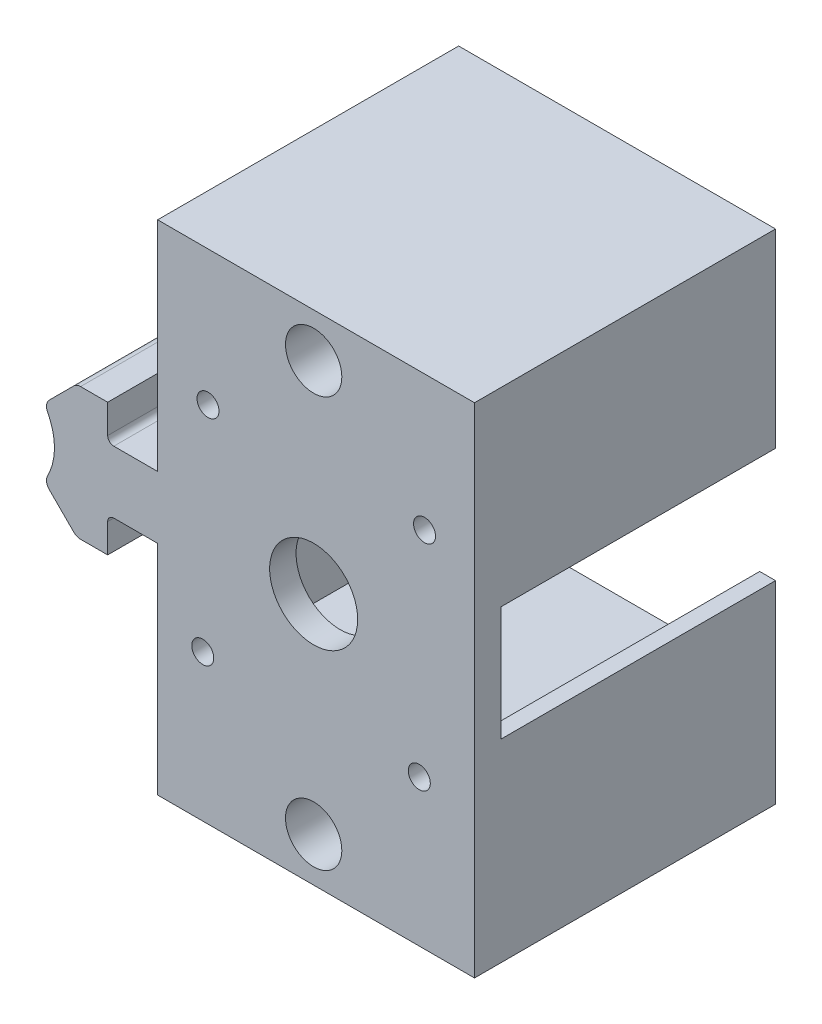
SolidWorks part; units mm, degrees
ref_plane "Front Plane" through (0, 0, 0) normal (0, 0, 1) x (1, 0, 0)
ref_plane "Top Plane" through (0, 0, 0) normal (0, 1, 0) x (1, 0, 0)
ref_plane "Right Plane" through (0, 0, 0) normal (1, 0, 0) x (0, 0, -1)
sketch "Sketch2" plane through (0, 0, 816.4924) normal (0, 0, 1) x (1, 0, 0)
  line L0 (35.7501, 34.0976) -> (35.7501, 33.2853)
  line L27 (48.1133, 38.1834) -> (50.6533, 38.1834)
  line L28 (50.6533, 38.1834) -> (50.6533, 56.9324)
  line L29 (50.6533, 56.9324) -> (52.6853, 56.9324)
  line L30 (52.6853, 56.9324) -> (52.6853, 10.4504)
  line L31 (52.6853, 10.4504) -> (50.6533, 10.4504)
  line L32 (50.6533, 10.4504) -> (50.6533, 29.1994)
  line L33 (50.6533, 29.1994) -> (48.1133, 29.1994)
  line L37 (44.3288, 29.1994) -> (48.1133, 29.1994)
  line L38 (43.4438, 24.1494) -> (43.4438, 28.3144)
  line L39 (39.5326, 24.1494) -> (43.4438, 24.1494)
  line L40 (35.016, 28.0957) -> (38.5589, 24.5527)
  line L41 (35.4657, 33.6914) -> (35.7501, 33.2853)
  line L42 (35.7501, 34.0976) -> (35.4657, 33.6914)
  line L43 (38.5589, 42.8301) -> (35.016, 39.2872)
  line L44 (43.4438, 43.2334) -> (39.5326, 43.2334)
  line L45 (43.4438, 39.0684) -> (43.4438, 43.2334)
  line L46 (48.1133, 38.1834) -> (44.3288, 38.1834)
  line L47 (44.3288, 29.1994) -> (48.1133, 29.1994)
  line L48 (43.4438, 24.1494) -> (43.4438, 28.3144)
  line L49 (39.5326, 24.1494) -> (43.4438, 24.1494)
  line L50 (35.016, 28.0957) -> (38.5589, 24.5527)
  line L53 (38.5589, 42.8301) -> (35.016, 39.2872)
  line L54 (43.4438, 43.2334) -> (39.5326, 43.2334)
  line L55 (43.4438, 39.0684) -> (43.4438, 43.2334)
  line L56 (48.1133, 38.1834) -> (44.3288, 38.1834)
  arc A38 (44.3288, 29.1994) -> (43.4438, 28.3144) centre (44.3288, 28.3144) ccw
  arc A39 (38.5589, 24.5527) -> (39.5326, 24.1494) centre (39.5326, 25.5264) ccw
  arc A40 (34.7724, 29.7132) -> (35.016, 28.0957) centre (35.9896, 29.0694) ccw
  arc A41 (34.7724, 29.7132) -> (35.7501, 33.2853) centre (27.2518, 33.6914) ccw
  arc A42 (35.7501, 34.0976) -> (34.7724, 37.6696) centre (27.2518, 33.6914) ccw
  arc A43 (35.016, 39.2872) -> (34.7724, 37.6696) centre (35.9896, 38.3135) ccw
  arc A44 (39.5326, 43.2334) -> (38.5589, 42.8301) centre (39.5326, 41.8564) ccw
  arc A45 (43.4438, 39.0684) -> (44.3288, 38.1834) centre (44.3288, 39.0684) ccw
  arc A46 (44.3288, 29.1994) -> (43.4438, 28.3144) centre (44.3288, 28.3144) ccw
  arc A47 (38.5589, 24.5527) -> (39.5326, 24.1494) centre (39.5326, 25.5264) ccw
  arc A48 (34.7724, 29.7132) -> (35.016, 28.0957) centre (35.9896, 29.0694) ccw
  arc A49 (34.7724, 29.7132) -> (35.7501, 33.2853) centre (27.2518, 33.6914) ccw
  arc A50 (35.7501, 34.0976) -> (34.7724, 37.6696) centre (27.2518, 33.6914) ccw
  arc A51 (35.016, 39.2872) -> (34.7724, 37.6696) centre (35.9896, 38.3135) ccw
  arc A52 (39.5326, 43.2334) -> (38.5589, 42.8301) centre (39.5326, 41.8564) ccw
  arc A53 (43.4438, 39.0684) -> (44.3288, 38.1834) centre (44.3288, 39.0684) ccw
  dimension "D2" = 46.482
  dimension "D3" = 2.032
  dimension "D4" = 2.54
  dimension "D1" = 0.508
extrude "Boss-Extrude1" add sketch "Sketch2" along normal blind 43.434
sketch "Sketch3" plane through (52.6853, 0, 0) normal (1, 0, 0) x (0, 0, -1)
  line L0 (-859.9264, 10.4504) -> (-816.4924, 10.4504) construction
  line L1 (-859.9264, 56.9324) -> (-856.1164, 56.9324)
  line L2 (-859.9264, 56.9324) -> (-859.9264, 10.4504)
  line L3 (-859.9264, 10.4504) -> (-856.1164, 10.4504)
  line L4 (-856.1164, 56.9324) -> (-856.1164, 10.4504)
  dimension "D1" = 3.81
extrude "Boss-Extrude2" add sketch "Sketch3" along normal blind 43.688
sketch "Sketch8" plane through (0, 0, 856.1164) normal (0, 0, -1) x (-1, 0, 0)
  line L0 (-52.6853, 10.4504) -> (-52.6853, 56.9324) construction
  line L1 (-96.3733, 56.9324) -> (-52.6853, 56.9324)
  line L2 (-96.3733, 56.9324) -> (-96.3733, 54.9004)
  line L3 (-94.0873, 54.9004) -> (-52.6853, 54.9004)
  line L4 (-52.6853, 56.9324) -> (-52.6853, 54.9004)
  line L6 (-96.3733, 10.4504) -> (-52.6853, 10.4504)
  line L7 (-96.3733, 10.4504) -> (-96.3733, 12.4824)
  line L8 (-94.0873, 12.4824) -> (-52.6853, 12.4824)
  line L9 (-52.6853, 10.4504) -> (-52.6853, 12.4824)
  line L11 (-96.3733, 54.9004) -> (-96.3733, 42.2204)
  line L12 (-96.3733, 42.2204) -> (-94.0873, 42.2204)
  line L13 (-94.0873, 54.9004) -> (-94.0873, 42.2204)
  line L15 (-96.3733, 12.4824) -> (-96.3733, 25.6904)
  line L16 (-96.3733, 25.6904) -> (-94.0873, 25.6904)
  line L17 (-94.0873, 12.4824) -> (-94.0873, 25.6904)
  dimension "D1" = 2.032
  dimension "D2" = 15.24
  dimension "D3" = 12.6801
  dimension "D5" = 2.286
  dimension "D6" = 2.032
extrude "Boss-Extrude5" add sketch "Sketch8" along direction (0, 0, 1) on the side of the normal up to surface (39.624 mm away)
sketch "Sketch9" plane through (0, 0, 859.9264) normal (0, 0, 1) x (1, 0, 0)
  circle A0 centre (73.1637, 34.1253) radius 6.35
  dimension "D1" = 12.7
extrude "Cut-Extrude1" cut sketch "Sketch9" against normal through all
sketch "Sketch10" plane through (0, 0, 856.1164) normal (0, 0, -1) x (-1, 0, 0)
  circle A0 centre (-89.1637, 50.1249) radius 1.5875
  circle A1 centre (-57.9217, 50.1464) radius 1.5875
  circle A2 centre (-57.1637, 18.9044) radius 1.5875
  circle A3 centre (-88.4057, 18.8829) radius 1.5875
  dimension "D1" = 3.175
  dimension "D2" = 31.242
  dimension "D3" = 31.242
  dimension "D4" = 31.242
  dimension "D5" = 31.242
extrude "Cut-Extrude2" cut sketch "Sketch10" against normal through all
sketch "Sketch12" plane through (0, 56.9324, 0) normal (0, 1, 0) x (1, 0, 0)
  line L1 (96.3733, -859.9264) -> (50.6533, -859.9264)
  line L2 (96.3733, -859.9264) -> (96.3733, -816.4924)
  line L3 (96.3733, -816.4924) -> (50.6533, -816.4924)
  line L4 (50.6533, -859.9264) -> (50.6533, -816.4924)
extrude "Boss-Extrude6" add sketch "Sketch12" along normal blind 12.7
sketch "Sketch13" plane through (0, 10.4504, 0) normal (0, -1, 0) x (1, 0, 0)
  line L1 (50.6533, 859.9264) -> (96.3733, 859.9264)
  line L2 (50.6533, 859.9264) -> (50.6533, 816.4924)
  line L3 (50.6533, 816.4924) -> (96.3733, 816.4924)
  line L4 (96.3733, 859.9264) -> (96.3733, 816.4924)
extrude "Boss-Extrude7" add sketch "Sketch13" along normal blind 12.7
sketch "Sketch14" plane through (0, 0, 859.9264) normal (0, 0, 1) x (1, 0, 0)
  line L0 (73.1637, 40.4753) -> (73.1637, 27.7753) construction
  line L1 (50.6533, 69.6324) -> (96.3733, 69.6324) construction
  line L2 (96.3733, -2.2496) -> (50.6533, -2.2496) construction
  line L3 (66.8137, 34.1253) -> (79.5137, 34.1253) construction
  circle A0 centre (73.1637, 63.2824) radius 4.064
  circle A1 centre (73.1637, 4.1004) radius 4.064
  circle A2 centre (73.1637, 34.1253) radius 6.35 construction
  point P16 (73.1637, 34.1253)
  dimension "D3" = 8.128
  dimension "D1" = 6.35
  dimension "D2" = 6.35
extrude "Cut-Extrude3" cut sketch "Sketch14" against normal blind 6.35
